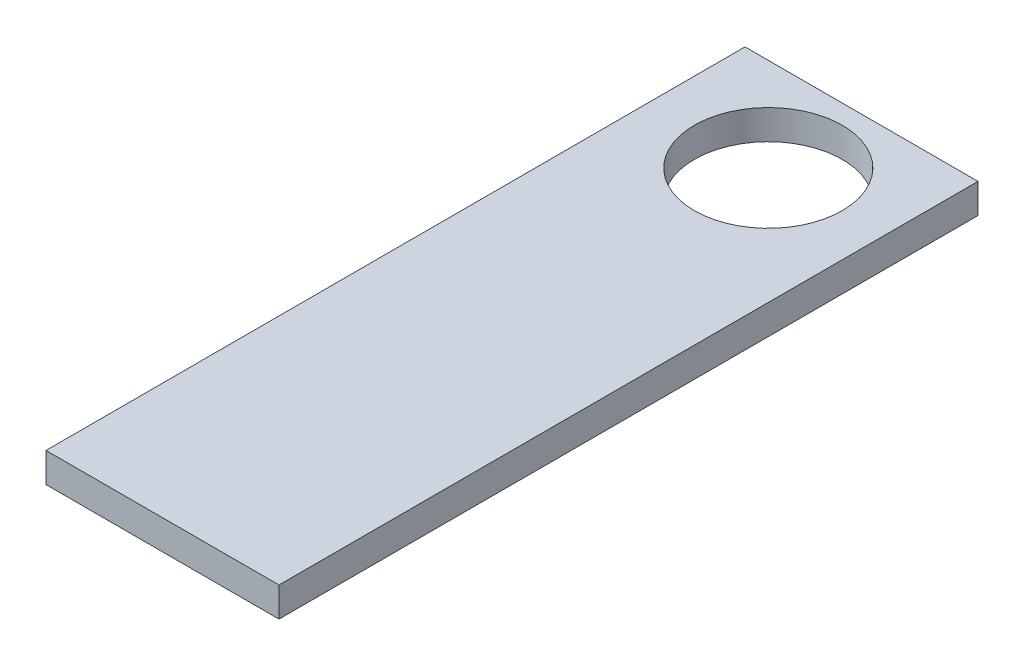
SolidWorks part; units mm, degrees
ref_plane "Front Plane" through (0, 0, 0) normal (0, 0, 1) x (1, 0, 0)
ref_plane "Top Plane" through (0, 0, 0) normal (0, 1, 0) x (1, 0, 0)
ref_plane "Right Plane" through (0, 0, 0) normal (1, 0, 0) x (0, 0, -1)
sketch "Sketch1" plane through (0, 0, 0) normal (0, 1, 0) x (1, 0, 0)
  line L0 (5, 0) -> (5, -30) construction
  line L1 (0, 0) -> (10, 0)
  line L2 (0, 0) -> (0, -30)
  line L3 (0, -30) -> (10, -30)
  line L4 (10, 0) -> (10, -30)
  circle A0 centre (5, -4) radius 3.175
  dimension "D3" = 6.35
  dimension "D1" = 10
  dimension "D2" = 30
  dimension "D4" = 4
extrude "Boss-Extrude1" add sketch "Sketch1" along normal blind 1.27
